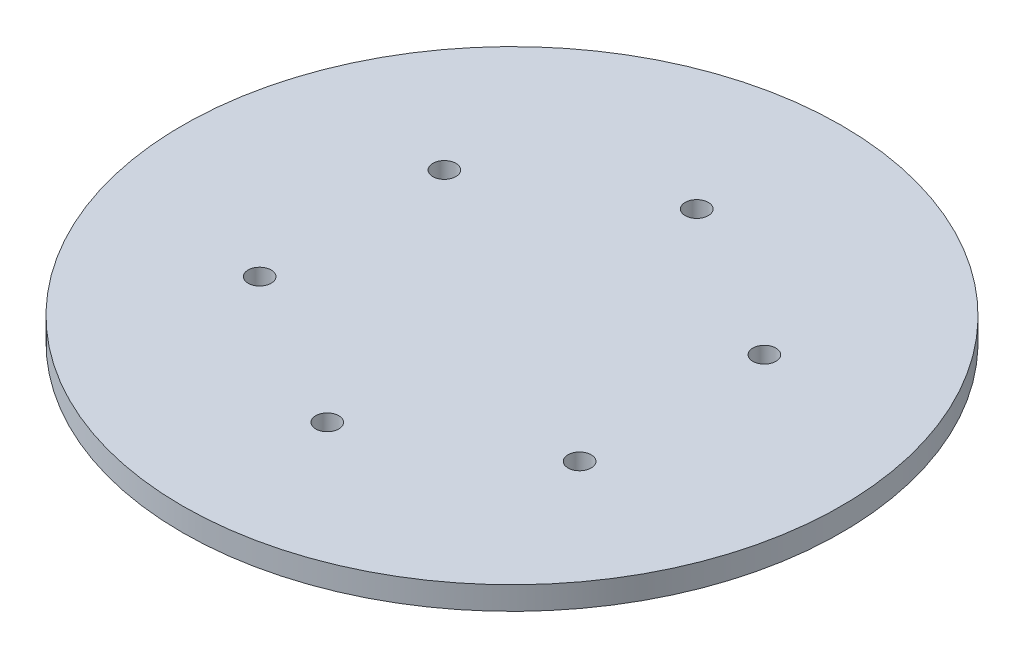
SolidWorks part; units mm, degrees
ref_plane "前视基准面" through (0, 0, 0) normal (0, 0, 1) x (1, 0, 0)
ref_plane "上视基准面" through (0, 0, 0) normal (0, 1, 0) x (1, 0, 0)
ref_plane "右视基准面" through (0, 0, 0) normal (1, 0, 0) x (0, 0, -1)
sketch "草图1" plane through (0, 0, 0) normal (0, 1, 0) x (1, 0, 0)
  circle A0 centre (0, 0) radius 142.711
  circle A1 centre (0, 80) radius 5
  circle A2 centre (69.282, 40) radius 5
  circle A3 centre (69.282, -40) radius 5
  circle A4 centre (0, -80) radius 5
  circle A5 centre (-69.282, -40) radius 5
  circle A6 centre (-69.282, 40) radius 5
  point P17 (0, 0)
  dimension "D1" = 10
  dimension "D2" = 80
  dimension "D3" = 6
extrude "凸台-拉伸1" add sketch "草图1" along normal blind 10
sketch "草图2" plane through (0, 10, 0) normal (0, 1, 0) x (1, 0, 0)
  text T0 "a1"
  text T1 "a2"
  text T2 "a3"
  text T3 "b1"
  text T4 "b2"
  text T5 "c"
  point P1 (10.266, 77.2103)
